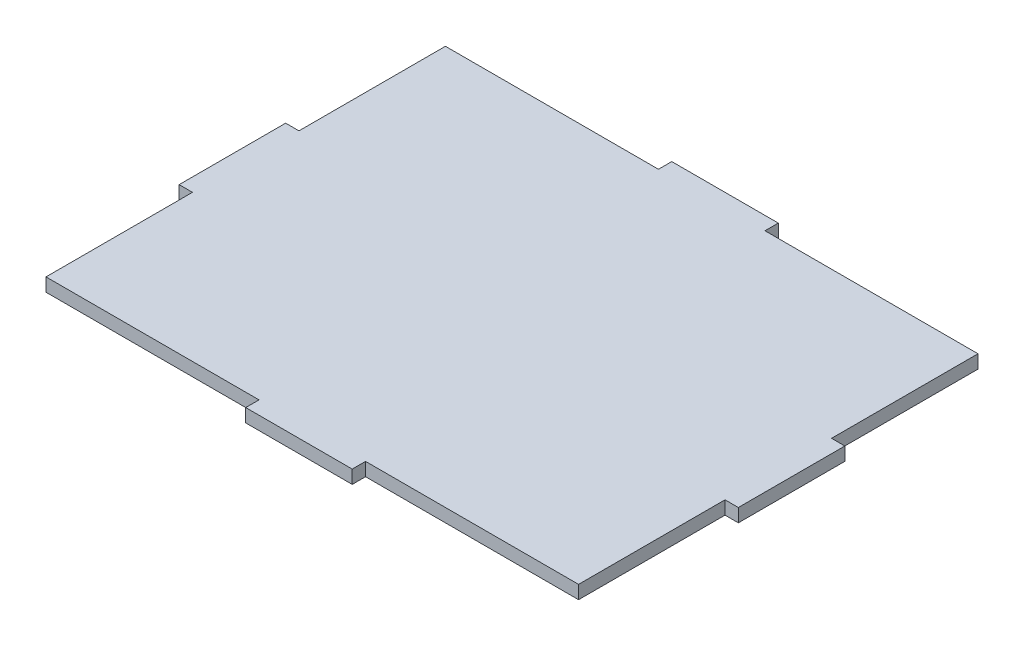
SolidWorks part; units mm, degrees
ref_plane "Front Plane" through (0, 0, 0) normal (0, 0, 1) x (1, 0, 0)
ref_plane "Top Plane" through (0, 0, 0) normal (0, 1, 0) x (1, 0, 0)
ref_plane "Right Plane" through (0, 0, 0) normal (1, 0, 0) x (0, 0, -1)
sketch "Sketch1" plane through (0, 0, 0) normal (0, 1, 0) x (1, 0, 0)
  line L1 (0.8759, 50.3621) -> (127.8759, 50.3621)
  line L2 (0.8759, 50.3621) -> (0.8759, -44.8879)
  line L3 (0.8759, -44.8879) -> (127.8759, -44.8879)
  line L4 (127.8759, 50.3621) -> (127.8759, -44.8879)
  dimension "D1" = 95.25
  dimension "D2" = 127
extrude "Boss-Extrude1" add sketch "Sketch1" along normal blind 3.175
sketch "Sketch2" plane through (127.8759, 0, 0) normal (1, 0, 0) x (0, 0, -1)
  line L0 (-44.8879, 3.175) -> (50.3621, 3.175) construction
  line L1 (-9.9629, 3.175) -> (15.4371, 3.175)
  line L2 (-9.9629, 3.175) -> (-9.9629, 0)
  line L3 (-9.9629, 0) -> (15.4371, 0)
  line L4 (15.4371, 3.175) -> (15.4371, 0)
  line L5 (-44.8879, 0) -> (50.3621, 0) construction
  line L6 (-44.8879, 3.175) -> (-44.8879, 0) construction
  line L9 (50.3621, 3.175) -> (50.3621, 0) construction
  dimension "D1" = 25.4
  dimension "D2" = 34.925
  dimension "D3" = 34.925
extrude "Boss-Extrude2" add sketch "Sketch2" along normal blind 3.175
sketch "Sketch3" plane through (0.8759, 0, 0) normal (-1, 0, 0) x (0, 0, 1)
  line L1 (9.9629, 3.175) -> (-15.4371, 3.175)
  line L2 (9.9629, 3.175) -> (9.9629, 0)
  line L3 (9.9629, 0) -> (-15.4371, 0)
  line L4 (-15.4371, 3.175) -> (-15.4371, 0)
extrude "Boss-Extrude3" add sketch "Sketch3" along normal blind 3.175
sketch "Sketch4" plane through (0, 0, -50.3621) normal (0, 0, -1) x (-1, 0, 0)
  line L0 (-127.8759, 3.175) -> (-0.8759, 3.175) construction
  line L1 (-51.6759, 3.175) -> (-77.0759, 3.175)
  line L2 (-51.6759, 3.175) -> (-51.6759, 0)
  line L3 (-51.6759, 0) -> (-77.0759, 0)
  line L4 (-77.0759, 3.175) -> (-77.0759, 0)
  line L5 (-127.8759, 0) -> (-0.8759, 0) construction
  line L6 (-0.8759, 3.175) -> (-0.8759, 0) construction
  dimension "D1" = 25.4
  dimension "D2" = 50.8
extrude "Boss-Extrude4" add sketch "Sketch4" along normal blind 3.175
sketch "Sketch5" plane through (0, 0, 44.8879) normal (0, 0, 1) x (1, 0, 0)
  line L1 (51.6759, 0) -> (77.0759, 0)
  line L2 (51.6759, 0) -> (51.6759, 3.175)
  line L3 (51.6759, 3.175) -> (77.0759, 3.175)
  line L4 (77.0759, 0) -> (77.0759, 3.175)
extrude "Boss-Extrude5" add sketch "Sketch5" along normal blind 3.175
